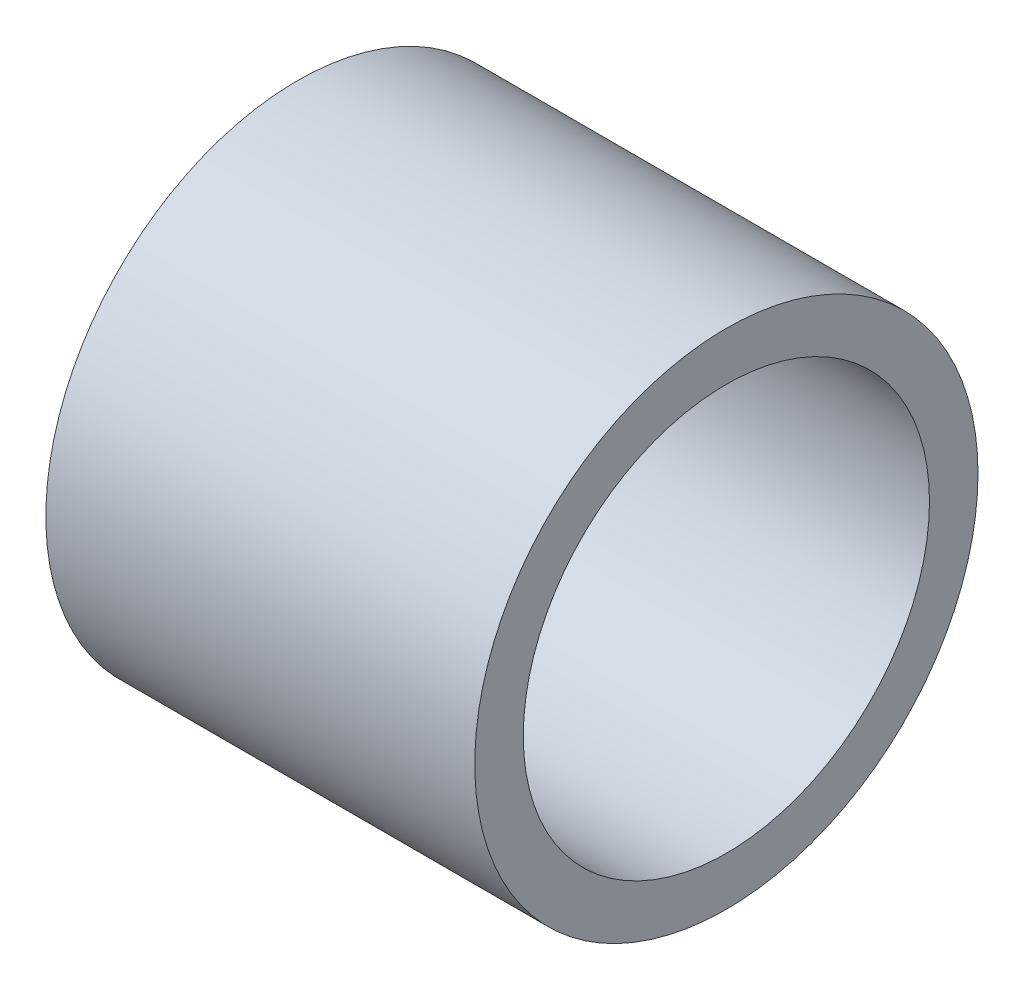
SolidWorks part; units mm, degrees
material "PET"
ref_plane "Front Plane" through (0, 0, 0) normal (0, 0, 1) x (1, 0, 0)
ref_plane "Top Plane" through (0, 0, 0) normal (0, 1, 0) x (1, 0, 0)
ref_plane "Right Plane" through (0, 0, 0) normal (1, 0, 0) x (0, 0, -1)
sketch "Sketch1" plane through (0, 0, 0) normal (1, 0, 0) x (0, 0, -1)
  circle A0 centre (0, 0) radius 8.382
  circle A1 centre (0, 0) radius 6.7659
  dimension "D1" = 16.764
  dimension "D2" = 13.5318
extrude "Boss-Extrude1" add sketch "Sketch1" along normal blind 14.2875
